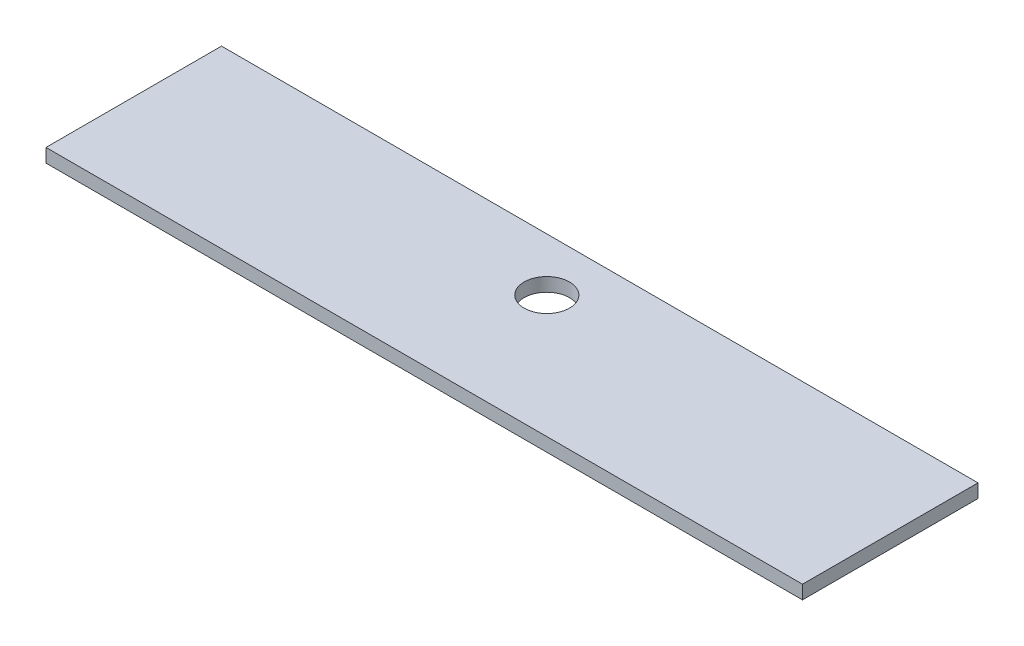
SolidWorks part; units mm, degrees
ref_plane "Front Plane" through (0, 0, 0) normal (0, 0, 1) x (1, 0, 0)
ref_plane "Top Plane" through (0, 0, 0) normal (0, 1, 0) x (1, 0, 0)
ref_plane "Right Plane" through (0, 0, 0) normal (1, 0, 0) x (0, 0, -1)
sketch "Sketch1" plane through (0, 0, 0) normal (0, 1, 0) x (1, 0, 0)
  line L1 (-83.5256, 39.1178) -> (916.4744, 39.1178)
  line L2 (-83.5256, 39.1178) -> (-83.5256, -192.8822)
  line L3 (-83.5256, -192.8822) -> (916.4744, -192.8822)
  line L4 (916.4744, 39.1178) -> (916.4744, -192.8822)
  line L5 (-83.5256, 39.1178) -> (916.4744, -192.8822) construction
  line L6 (-83.5256, -192.8822) -> (916.4744, 39.1178) construction
  point P0 (416.4744, -76.8822)
  dimension "D1" = 1000
  dimension "D2" = 232
extrude "Boss-Extrude1" add sketch "Sketch1" along normal blind 18
sketch "Sketch2" plane through (0, 18, 0) normal (0, 1, 0) x (1, 0, 0)
  line L0 (416.4744, 39.1178) -> (416.4744, -125.0787) construction
  line L1 (916.4744, 39.1178) -> (-83.5256, 39.1178) construction
  circle A0 centre (416.4744, -30.8822) radius 30
  dimension "D1" = 60
  dimension "D2" = 70
extrude "Cut-Extrude1" cut sketch "Sketch2" against normal up to surface (18 mm away) from surface at 0 up to face at (416.4744, 0, 76.8822) starting at face at (416.4744, 18, 76.8822)
